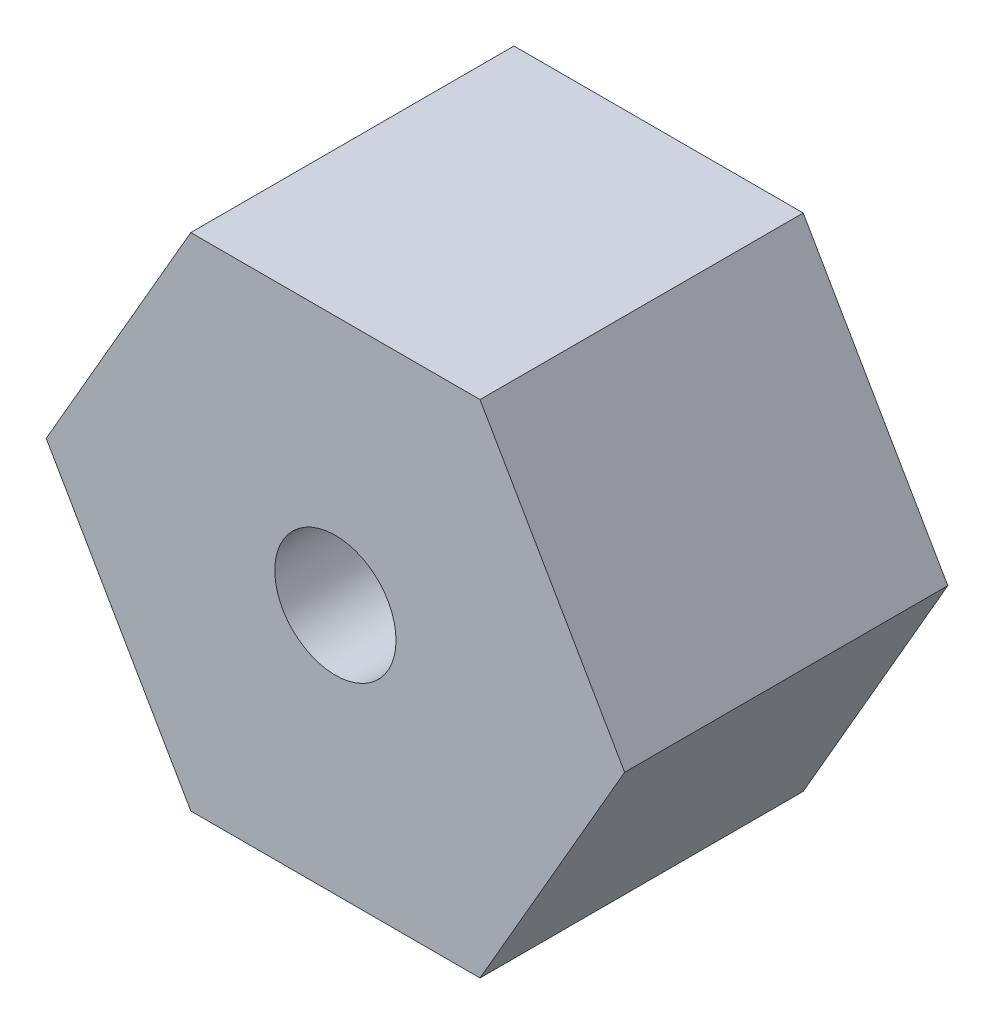
SolidWorks part; units mm, degrees
ref_plane "Front Plane" through (0, 0, 0) normal (0, 0, 1) x (1, 0, 0)
ref_plane "Top Plane" through (0, 0, 0) normal (0, 1, 0) x (1, 0, 0)
ref_plane "Right Plane" through (0, 0, 0) normal (1, 0, 0) x (0, 0, -1)
sketch "Sketch1" plane through (0, 0, 0) normal (0, 0, 1) x (1, 0, 0)
  line L0 (-3.5796, 6.2) -> (3.5796, 6.2)
  line L1 (3.5796, 6.2) -> (7.1591, 0)
  line L2 (7.1591, 0) -> (3.5796, -6.2)
  line L3 (3.5796, -6.2) -> (-3.5796, -6.2)
  line L4 (-3.5796, -6.2) -> (-7.1591, 0)
  line L5 (-7.1591, 0) -> (-3.5796, 6.2)
  circle A0 centre (0, 0) radius 7.1591 construction
  circle A1 centre (0, 0) radius 1.5
  point P6 (0, 0)
  dimension "D2" = 3
  dimension "D1" = 12.4
extrude "Main" add sketch "Sketch1" along normal blind 8
